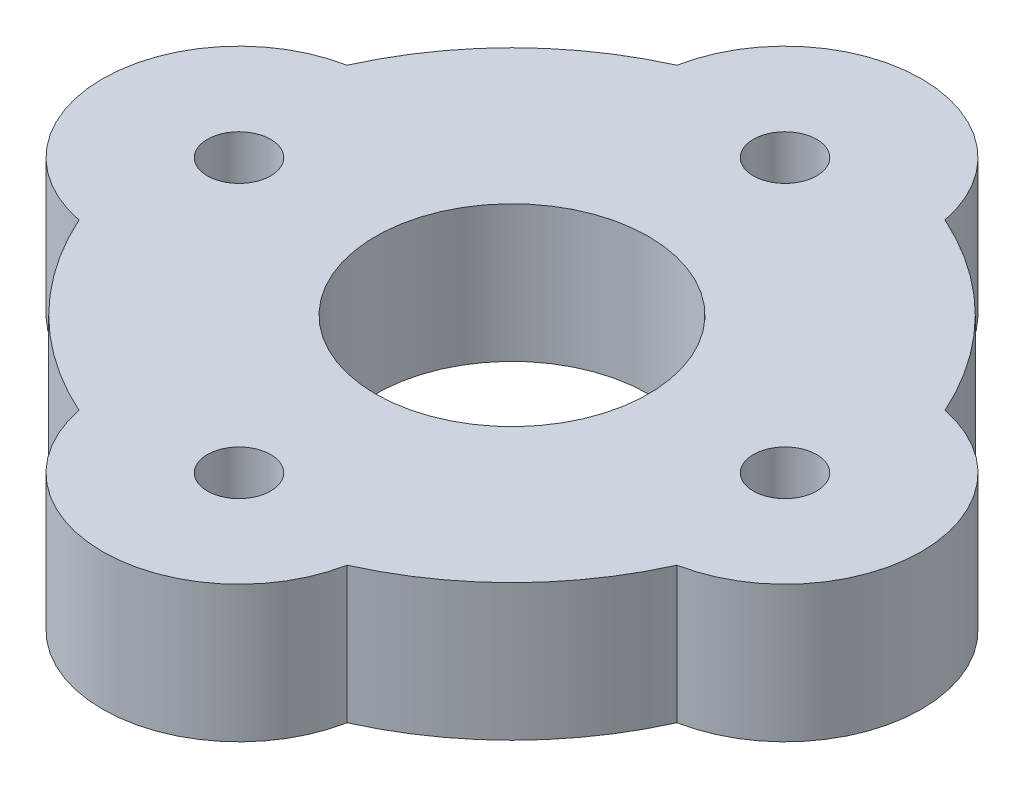
SolidWorks part; units mm, degrees
ref_plane "Front Plane" through (0, 0, 0) normal (0, 0, 1) x (1, 0, 0)
ref_plane "Top Plane" through (0, 0, 0) normal (0, 1, 0) x (1, 0, 0)
ref_plane "Right Plane" through (0, 0, 0) normal (1, 0, 0) x (0, 0, -1)
sketch "Sketch1" plane through (0, 0, 0) normal (0, 1, 0) x (1, 0, 0)
  line L0 (15.7607, 0) -> (-15.7607, 0) construction
  line L4 (0, 2.1324) -> (0, -2.9835) construction
  circle A0 centre (0, 0) radius 12.7 construction
  circle A1 centre (0, 12.7) radius 1.4732 construction
  circle A3 centre (0, 0) radius 14.1732 construction
  circle A4 centre (0, 0) radius 6.35
  circle A5 centre (12.7, 0) radius 1.4732 construction
  circle A6 centre (0, -12.7) radius 1.4732 construction
  circle A8 centre (22.225, 0) radius 4.7625 construction
  circle A9 centre (-22.225, 0) radius 4.7625 construction
  circle A10 centre (-12.7, 0) radius 1.4732 construction
  circle A11 centre (0, 0) radius 15.24
  circle A12 centre (-12.7, 0) radius 1.4732 construction
  point P17 (0, 0)
  dimension "D1" = 25.4
  dimension "D2" = 2.9464
  dimension "D3" = 30.48
  dimension "D4" = 12.7
  dimension "D7" = 9.525
  dimension "D5" = 4
  dimension "D9" = 44.45
extrude "Boss-Extrude1" add sketch "Sketch1" along normal blind 6.35
hole_wizard "#4 Clearance Hole1" positions "Sketch3" profile "Sketch2" hole size "#4" standard "ANSI Inch" end condition up to next
sketch "Sketch3" plane through (-8.0155, 6.35, -5.0661) normal (0, 1, 0) x (1, 0, 0)
  point P11 (8.0155, 7.6339)
  point P15 (-4.6845, -5.0661)
  point P18 (20.7155, -5.0661)
  point P21 (8.0155, -17.7661)
sketch "Sketch2" plane through (0, 6.35, -12.7) normal (1, 0, 0) x (0, 0, 1)
  line L0 (0, 0) -> (0, 6.35)
  line L1 (0, 6.35) -> (1.4732, 6.35)
  line L2 (1.4732, 6.35) -> (1.4732, 0)
  line L5 (1.4732, 0) -> (0, 0)
  line L11 (0, -6.35) -> (0, 107.95) construction
  dimension "Thru Hole Dia." = 2.9464
  dimension "Thru Hole Depth" = 6.35
hole_wizard "3/8 (0.375) Diameter Hole1" positions "Sketch5" profile "Sketch4" hole size "3/8" standard "ANSI Inch"
sketch "Sketch5" plane through (0, 6.35, 0) normal (0, 1, 0) x (-1, 0, 0)
  point P0 (22.225, 0)
  point P3 (-22.225, 0)
sketch "Sketch4" plane through (-22.225, 6.35, 0) normal (1, 0, 0) x (0, 0, 1)
  line L0 (0, 0) -> (0, 6.35)
  line L1 (0, 6.35) -> (4.7625, 6.35)
  line L2 (4.7625, 6.35) -> (4.7625, 0)
  line L5 (4.7625, 0) -> (0, 0)
  line L11 (0, -6.35) -> (0, 107.95) construction
  dimension "Thru Hole Dia." = 9.525
  dimension "Thru Hole Depth" = 6.35
sketch "Sketch7" plane through (0, 6.35, 0) normal (0, 1, 0) x (1, 0, 0)
  arc A1 (-6.2343, 13.9065) -> (6.2343, 13.9065) centre (0, 12.7) cw
  circle A3 centre (0, 0) radius 15.24 construction
  arc A4 (6.2343, 13.9065) -> (-6.2343, 13.9065) centre (0, 0) ccw
  dimension "D1" = 6.35
extrude "Boss-Extrude2" add sketch "Sketch7" against normal up to surface (6.35 mm away) up to face at (0, 0, -11.2268)
pattern_circular "CirPattern1" count 4 over 360 about axis through (0, 0, 0) along (0, 1, 0) of "Boss-Extrude2"
